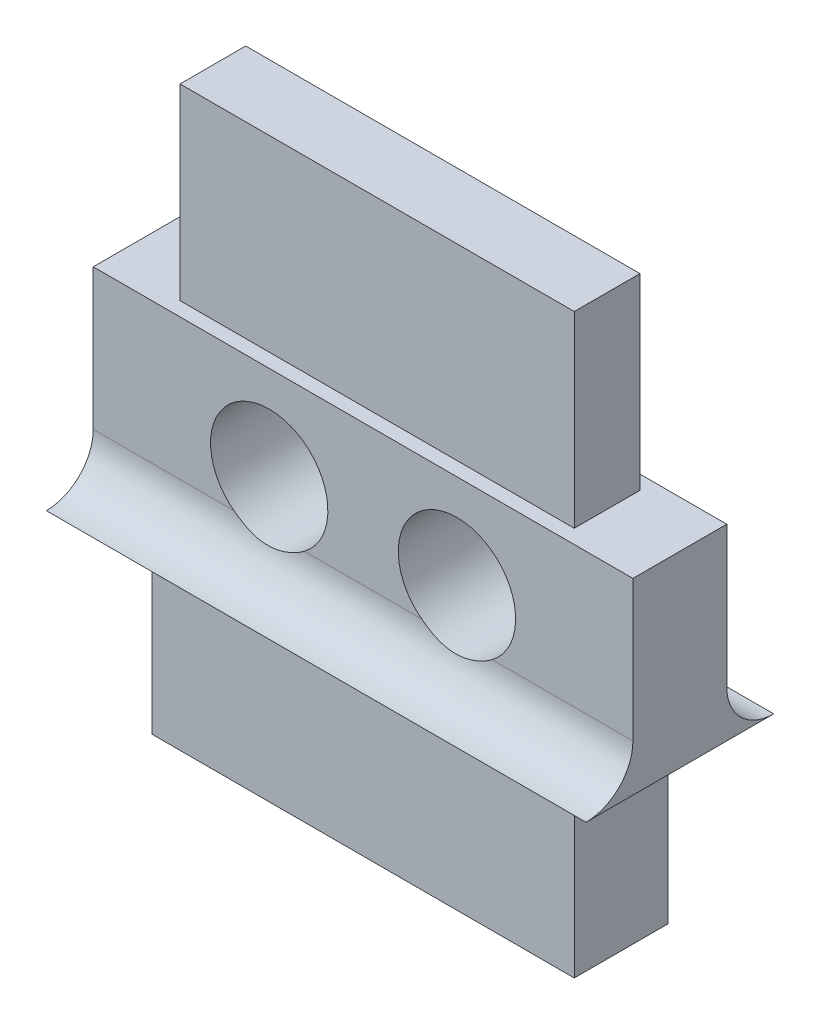
SolidWorks part; units mm, degrees
ref_plane "Front Plane" through (0, 0, 0) normal (0, 0, 1) x (1, 0, 0)
ref_plane "Top Plane" through (0, 0, 0) normal (0, 1, 0) x (1, 0, 0)
ref_plane "Right Plane" through (0, 0, 0) normal (1, 0, 0) x (0, 0, -1)
sketch "Model" plane through (0, 0, 0) normal (0, 0, 1) x (1, 0, 0)
  line L0 (5.7504, 12) -> (5.7504, 0) construction
  line L37 (1.25, 4) -> (0, 4)
  line L38 (10.2507, 4) -> (11.5007, 4)
  line L39 (1.25, 0) -> (10.2507, 0)
  line L40 (1.25, 4) -> (1.25, 0)
  line L41 (10.2507, 4) -> (10.2507, 0)
  line L126 (10.2507, 8) -> (11.5007, 8)
  line L127 (1.25, 8) -> (0, 8)
  line L128 (10.2507, 12) -> (1.25, 12)
  line L129 (10.2507, 8) -> (10.2507, 12)
  line L130 (1.25, 8) -> (1.25, 12)
  line L131 (0, 8) -> (0, 4)
  line L132 (11.5007, 8) -> (11.5007, 4)
  circle A81 centre (7.7507, 6) radius 1.25
  circle A82 centre (3.75, 6) radius 1.25
  dimension "D1" = 2.5
  dimension "D2" = 2
  dimension "D3" = 2.5
  dimension "D4" = 9.0007
  dimension "D5" = 4
  dimension "D6" = 2.5
extrude "Boss-Extrude1" add sketch "Model" along normal blind 2
sketch "Sketch1" plane through (0, 0, 0) normal (-1, 0, 0) x (0, 0, 1)
  line L0 (1, 0) -> (1, 7) construction
  line L1 (2, 4) -> (2, 5)
  line L2 (2, 4) -> (3, 4)
  line L3 (0, 4) -> (-1, 4)
  line L4 (0, 4) -> (0, 5)
  arc A0 (2, 5) -> (3, 4) centre (3, 5) ccw
  arc A1 (0, 5) -> (-1, 4) centre (-1, 5) cw
  dimension "D1" = 1
  dimension "D2" = 1
  dimension "D3" = 4
  dimension "D4" = 1
  dimension "D5" = 2
extrude "Boss-Extrude2" add sketch "Sketch1" against normal up to surface (11.5007 mm away) up to face at (11.5007, 6, 1)
sketch "Sketch2" plane through (0, 0, 2) normal (0, 0, 1) x (1, 0, 0)
  line L0 (5.7504, 12) -> (5.7504, 0) construction
  line L1 (10.2507, 12) -> (1.25, 12) construction
  line L2 (1.25, 0) -> (10.2507, 0) construction
  circle A0 centre (3.75, 6) radius 1.25
  circle A1 centre (7.7507, 6) radius 1.25
  dimension "D1" = 2.5
extrude "Cut-Extrude1" cut sketch "Sketch2" against normal through all both and the other way through all
sketch "Sketch3" plane through (0, 12, 0) normal (0, 1, 0) x (1, 0, 0)
  line L1 (10.2507, 0) -> (1.25, 0)
  line L2 (10.2507, 0) -> (10.2507, -2)
  line L3 (10.2507, -2) -> (1.25, -2)
  line L4 (1.25, 0) -> (1.25, -2)
  line L5 (9.9507, -0.3) -> (1.55, -0.3)
  line L6 (9.9507, -0.3) -> (9.9507, -1.7)
  line L7 (9.9507, -1.7) -> (1.55, -1.7)
  line L8 (1.55, -0.3) -> (1.55, -1.7)
  dimension "D1" = 0.3
  dimension "D2" = 0.3
  dimension "D3" = 0.3
  dimension "D4" = 0.3
extrude "Cut-Extrude2" cut sketch "Sketch3" against normal blind 4
equation "\"D4@Model\"= \"fingerWidth@parametersSketch@prostheticParameters.SLDPRT\" * 0.5556"
equation "\"D2@Sketch3\"=\"tol2@parametersSketch@prostheticParameters.SLDPRT\""
equation "\"D1@Sketch3\"=\"tol2@parametersSketch@prostheticParameters.SLDPRT\""
equation "\"D3@Sketch3\"=\"tol2@parametersSketch@prostheticParameters.SLDPRT\""
equation "\"D4@Sketch3\"=\"tol2@parametersSketch@prostheticParameters.SLDPRT\""
